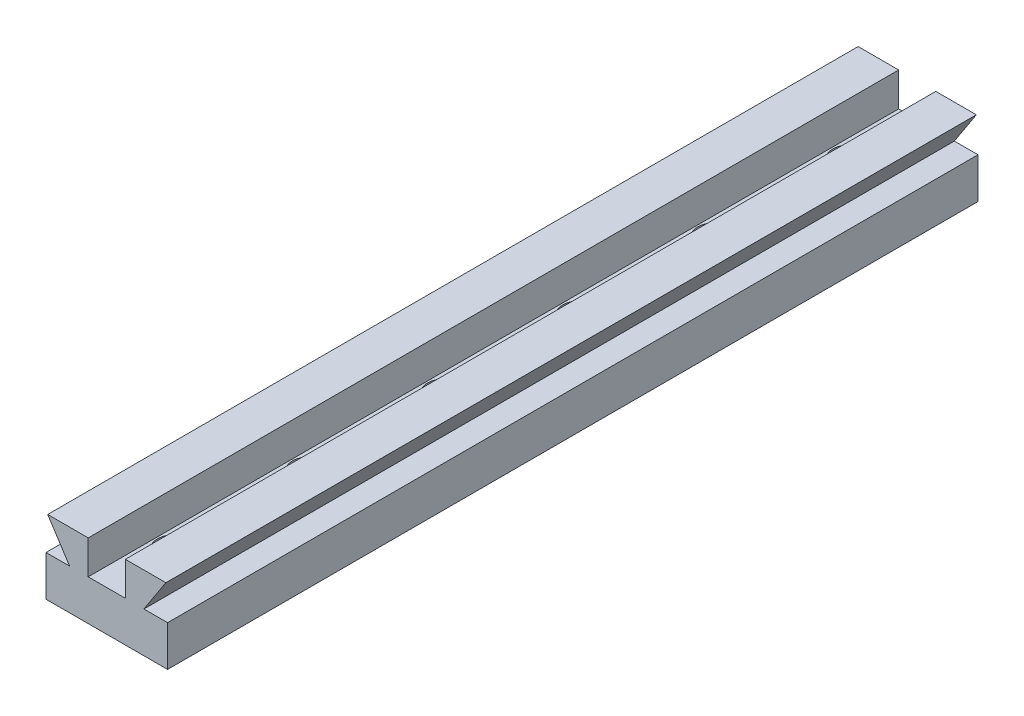
SolidWorks part; units mm, degrees
ref_plane "Front Plane" through (0, 0, 0) normal (0, 0, 1) x (1, 0, 0)
ref_plane "Top Plane" through (0, 0, 0) normal (0, 1, 0) x (1, 0, 0)
ref_plane "Right Plane" through (0, 0, 0) normal (1, 0, 0) x (0, 0, -1)
sketch "Sketch1" plane through (0, 0, 0) normal (0, 0, 1) x (1, 0, 0)
  line L0 (-9.6002, 1.4137) -> (-3.6002, 1.4137)
  line L1 (-3.6002, 1.4137) -> (-3.6002, -3.5863)
  line L2 (-3.6002, -3.5863) -> (1.8998, -3.5863)
  line L3 (1.8998, -3.5863) -> (1.8998, 1.4137)
  line L4 (1.8998, 1.4137) -> (7.8998, 1.4137)
  line L5 (7.8998, 1.4137) -> (4.6498, -3.5863)
  line L6 (4.6498, -3.5863) -> (8.1498, -3.5863)
  line L7 (8.1498, -3.5863) -> (8.1498, -9.5863)
  line L8 (8.1498, -9.5863) -> (-9.8502, -9.5863)
  line L9 (-9.8502, -9.5863) -> (-9.8502, -3.5863)
  line L10 (-9.8502, -3.5863) -> (-6.3502, -3.5863)
  line L11 (-6.3502, -3.5863) -> (-9.6002, 1.4137)
  point P2 (-0.8502, -3.5863)
  point P13 (-0.8502, -9.5863)
  dimension "D1" = 18
  dimension "D2" = 6
  dimension "D3" = 6
  dimension "D4" = 6
  dimension "D5" = 6
  dimension "D6" = 5.5
  dimension "D7" = 3.5
  dimension "D8" = 3.5
  dimension "D9" = 5
  dimension "D10" = 5
extrude "Boss-Extrude1" add sketch "Sketch1" along normal blind 120
sketch "Sketch2" plane through (0, -3.5863, 0) normal (0, 1, 0) x (1, 0, 0)
  line L0 (1.8998, 0) -> (-3.6002, 0) construction
  circle A0 centre (-0.8502, -10) radius 2.5
  circle A1 centre (-0.8502, -30) radius 2.5
  circle A2 centre (-0.8502, -50) radius 2.5
  circle A3 centre (-0.8502, -70) radius 2.5
  circle A4 centre (-0.8502, -90) radius 2.5
  circle A5 centre (-0.8502, -110) radius 2.5
  point P12 (0, 0)
  point P15 (-0.8502, 0)
  dimension "D1" = 5
  dimension "D2" = 20
  dimension "D3" = 10
  dimension "D4" = 20
  dimension "D5" = 20
  dimension "D6" = 20
  dimension "D7" = 20
extrude "Cut-Extrude1" cut sketch "Sketch2" against normal blind 2.5
sketch "Sketch3" plane through (0, -6.0863, 0) normal (0, 1, 0) x (1, 0, 0)
  circle A0 centre (-0.8502, -10) radius 1.5
  circle A1 centre (-0.8502, -30) radius 1.5
  circle A2 centre (-0.8502, -50) radius 1.5
  circle A3 centre (-0.8502, -70) radius 1.5
  circle A4 centre (-0.8502, -90) radius 1.5
  circle A5 centre (-0.8502, -110) radius 1.5
  dimension "D1" = 3
extrude "Cut-Extrude2" cut sketch "Sketch3" against normal through all
